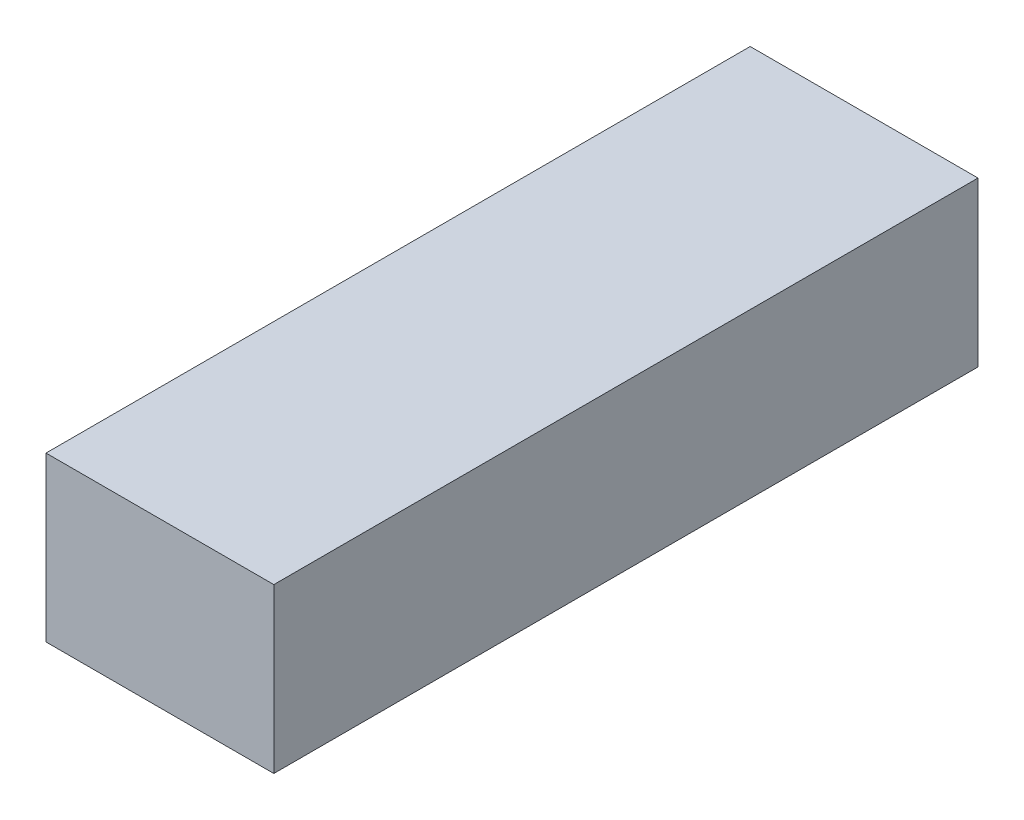
SolidWorks part; units mm, degrees
ref_plane "Front Plane" through (0, 0, 0) normal (0, 0, 1) x (1, 0, 0)
ref_plane "Top Plane" through (0, 0, 0) normal (0, 1, 0) x (1, 0, 0)
ref_plane "Right Plane" through (0, 0, 0) normal (1, 0, 0) x (0, 0, -1)
sketch "Sketch1" plane through (0, 0, 0) normal (0, 0, 1) x (1, 0, 0)
  line L1 (-22, -15.8) -> (22, -15.8)
  line L2 (-22, -15.8) -> (-22, 15.8)
  line L3 (-22, 15.8) -> (22, 15.8)
  line L4 (22, -15.8) -> (22, 15.8)
  line L5 (-22, -15.8) -> (22, 15.8) construction
  line L6 (-22, 15.8) -> (22, -15.8) construction
  point P0 (0, 0)
  dimension "D1" = 44
  dimension "D2" = 31.6
extrude "Boss-Extrude1" add sketch "Sketch1" along normal blind 136
